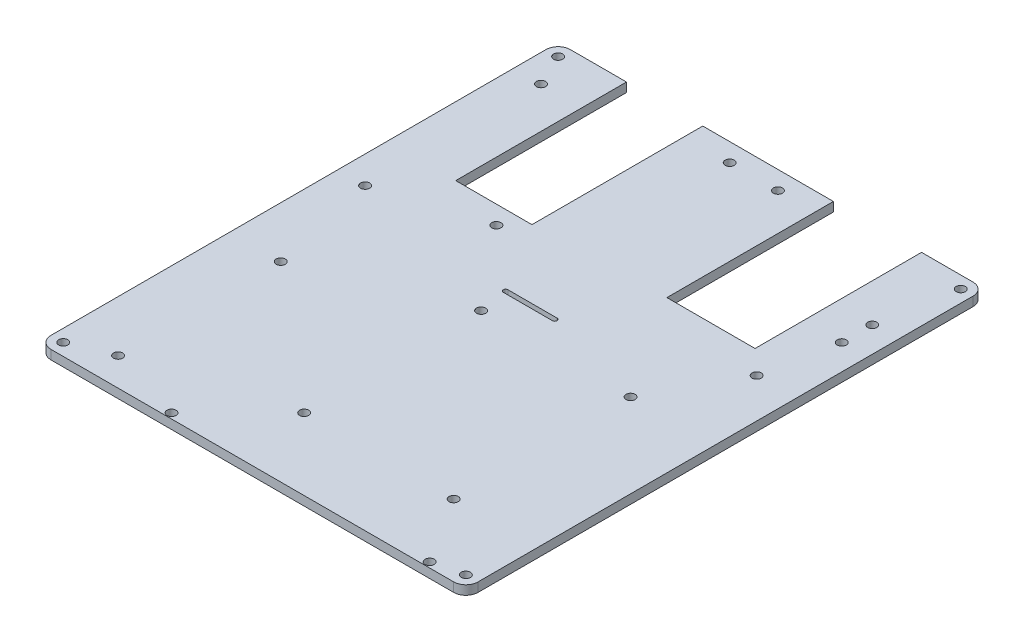
SolidWorks part; units mm, degrees
material "Beech"
ref_plane "Front Plane" through (0, 0, 0) normal (0, 0, 1) x (1, 0, 0)
ref_plane "Top Plane" through (0, 0, 0) normal (0, 1, 0) x (1, 0, 0)
ref_plane "Right Plane" through (0, 0, 0) normal (1, 0, 0) x (0, 0, -1)
sketch "Sketch1" plane through (0, 0, 0) normal (0, 1, 0) x (1, 0, 0)
  line L0 (-4, 0) -> (-136, 0)
  line L1 (-140, 4) -> (-140, 166.2534)
  line L3 (0, 166.2534) -> (0, 4)
  line L4 (-4, 170.2534) -> (-20.8604, 170.2534)
  line L5 (-20.8604, 170.2534) -> (-20.8604, 115.6653)
  line L6 (-20.8604, 115.6653) -> (-49.7543, 115.6653)
  line L7 (-49.7543, 115.6653) -> (-49.7543, 170.2534)
  line L8 (-49.7543, 170.2534) -> (-92.5881, 170.2534)
  line L9 (-92.5881, 170.2534) -> (-92.5881, 114.2611)
  line L11 (-78.0537, 91.0922) -> (-61.9463, 91.0922) construction
  line L13 (-117.5881, 170.2534) -> (-136, 170.2534)
  line L14 (-52.38, 0.2271) -> (-52.38, 170.2534) construction
  line L32 (-117.5881, 170.2534) -> (-117.5881, 114.2611)
  line L37 (-70, 0) -> (-70, 170.2534) construction
  line L38 (-78.0537, 91.8419) -> (-61.9463, 91.8419)
  line L43 (-78.0537, 90.3424) -> (-61.9463, 90.3424)
  line L45 (-117.5881, 114.2611) -> (-92.5881, 114.2611)
  arc A0 (-136, 0) -> (-140, 4) centre (-136, 4) cw
  arc A1 (-4, 0) -> (0, 4) centre (-4, 4) ccw
  arc A2 (-4, 170.2534) -> (0, 166.2534) centre (-4, 166.2534) cw
  arc A3 (-140, 166.2534) -> (-136, 170.2534) centre (-136, 166.2534) cw
  circle A4 centre (-136, 166.2534) radius 1.5
  circle A5 centre (-4, 166.2534) radius 1.5
  circle A6 centre (-136, 4) radius 1.5
  circle A7 centre (-4, 4) radius 1.5
  circle A12 centre (-8.3604, 141.5903) radius 1.5
  circle A13 centre (-8.3604, 131.5903) radius 1.5
  circle A21 centre (-123.2655, 62.5775) radius 1.5
  circle A22 centre (-123.2655, 9.2469) radius 1.5
  circle A32 centre (-61.9463, 164.2534) radius 1.5
  circle A33 centre (-77.7545, 164.2534) radius 1.5
  circle A34 centre (-131.022, 155.6607) radius 1.5
  circle A35 centre (-131.022, 97.9927) radius 1.5
  circle A38 centre (-27.5, 81.5) radius 1.5
  circle A39 centre (-76.5, 81.5) radius 1.5
  circle A40 centre (-27.5, 23.5) radius 1.5
  circle A41 centre (-76.5, 23.5) radius 1.5
  arc A44 (-78.0537, 91.8419) -> (-78.0537, 90.3424) centre (-78.0537, 91.0922) ccw
  arc A45 (-61.9463, 90.3424) -> (-61.9463, 91.8419) centre (-61.9463, 91.0922) ccw
  circle A46 centre (-98.25, 108.25) radius 1.5
  circle A47 centre (-12.9198, 108.25) radius 1.5
  circle A48 centre (-98.25, 1.75) radius 1.5
  circle A49 centre (-13.616, 1.75) radius 1.5
  point P7 (-140, 0)
  point P10 (0, 0)
  point P13 (0, 170)
  point P16 (-140, 170)
  point P40 (-70, 91.0922)
  point P109 (-117.5881, 93.0998)
  point P123 (-31.2261, 125.3974)
  dimension "D3" = 4
  dimension "D1" = 140
  dimension "D2" = 170
extrude "Boss-Extrude1" add sketch "Sketch1" along normal blind 3
